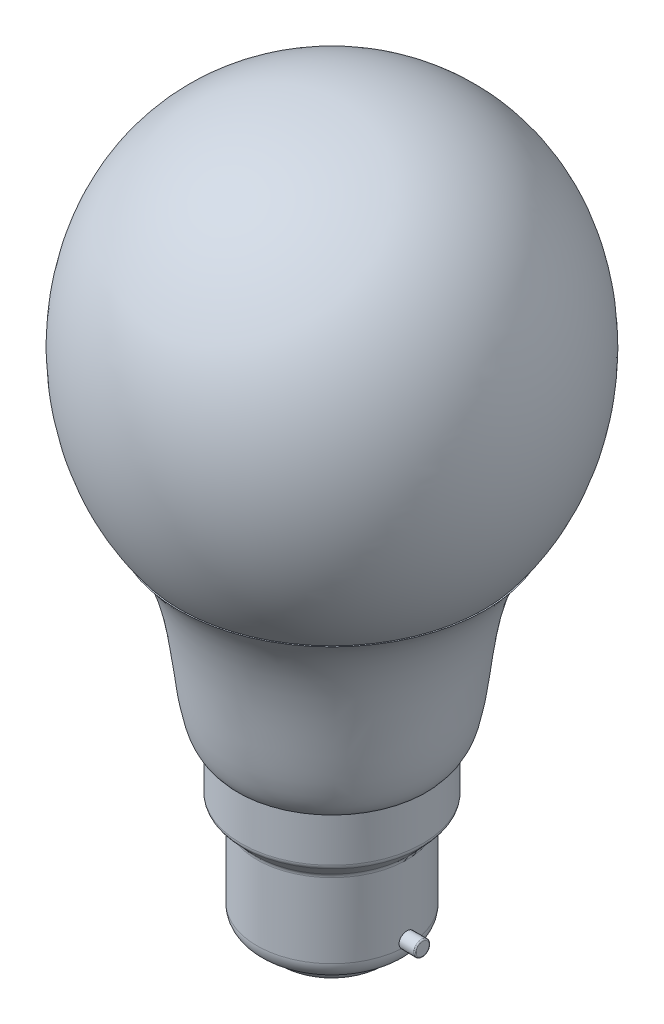
SolidWorks part; units mm, degrees
ref_plane "Front Plane" through (0, 0, 0) normal (0, 0, 1) x (1, 0, 0)
ref_plane "Top Plane" through (0, 0, 0) normal (0, 1, 0) x (1, 0, 0)
ref_plane "Right Plane" through (0, 0, 0) normal (1, 0, 0) x (0, 0, -1)
sketch "Sketch1" plane through (0, 0, 0) normal (0, 0, 1) x (1, 0, 0)
  line L0 (-312.7536, 342.4742) -> (-290.7536, 342.4742) construction
  line L1 (-11.0043, 13.5815) -> (10.9957, 13.5815) construction
  dimension "D1" = 22
  dimension "D2" = 22
sketch "Sketch2" plane through (0, 0, 0) normal (0, 0, 1) x (1, 0, 0)
  line L0 (0, 0) -> (0, 30)
  line L1 (0, 30) -> (0, 118)
  line L2 (0, 30) -> (15, 30)
  line L3 (15, 30) -> (19.4, 34.3) construction
  line L4 (19.4, 34.3) -> (16.4, 51.5) construction
  line L5 (16.4, 51.5) -> (24.5115, 60) construction
  line L6 (24.5115, 60) -> (0, 60)
  line L7 (0, 60) -> (0, 30)
  spline S0 degree 3 poles (15, 30) (19.4, 34.3) (16.4, 51.5) (24.5115, 60) knots 0 0 0 0 1 1 1 1
  point P8 (12.2557, 60)
  point P9 (0, 0)
  point P11 (0.6623, 30)
  dimension "D5" = 32
  dimension "D1" = 30
  dimension "D2" = 88
  dimension "D3" = 15
  dimension "D4" = 30
  dimension "D6" = 4.3
  dimension "D7" = 16.4
  dimension "D8" = 19.4
  dimension "D9" = 21.5
revolve "Revolve2" add sketch "Sketch2" angle 360 about L1
sketch "Sketch4" plane through (0, 0, 0) normal (0, 0, 1) x (1, 0, 0)
  line L0 (0, 60) -> (0, 118)
  line L1 (24.5115, 60) -> (-24.5115, 60) construction
  line L2 (0, 60) -> (24.3, 60)
  line L3 (0, 118) -> (32.9621, 118) construction
  line L4 (32.9621, 118) -> (40, 80) construction
  line L5 (40, 80) -> (24.3, 60) construction
  spline S0 degree 3 poles (0, 118) (32.9621, 118) (40, 80) (24.3, 60) knots 0 0 0 0 1 1 1 1
  point P8 (31.2763, 119.4939)
  point P9 (39.6236, 79.0706)
  point P10 (32.7636, 118.3221)
  point P11 (0, 0)
  point P12 (39.8683, 79.9908)
  point P15 (11.1368, 60)
  point P16 (0, 112.3974)
  point P17 (0, 68.5441)
  point P18 (0, 79.8107)
  point P19 (1.3785, 60)
  dimension "D3" = 78.5
  dimension "D1" = 58
  dimension "D2" = 24.3
  dimension "D4" = 58
  dimension "D5" = 20
  dimension "D6" = 40
revolve "Revolve3" add sketch "Sketch4" angle 360 about L0
sketch "Sketch5" plane through (0, 0, 0) normal (0, 0, 1) x (1, 0, 0)
  line L0 (0, 0) -> (0, 30)
  line L1 (-15, 30) -> (15, 30) construction
  line L2 (0, 30) -> (14.5, 30)
  line L3 (14.5, 30) -> (14.5, 22.3)
  line L4 (14.5, 22.3) -> (12, 19.6)
  line L5 (12, 19.6) -> (12, 7.3)
  line L6 (0, 4.3) -> (9, 4.3)
  line L7 (0, 2) -> (6.4924, 2)
  arc A0 (9, 4.3) -> (12, 7.3) centre (9, 7.3) ccw
  arc A1 (6.4924, 2) -> (9, 4.3) centre (6.4924, 4.5169) ccw
  dimension "D1" = 7.7
  dimension "D2" = 14.5
  dimension "D3" = 12
  dimension "D4" = 10.4
  dimension "D5" = 9
  dimension "D6" = 4.3
  dimension "D7" = 2.3
revolve "Revolve4" add sketch "Sketch5" angle 360 about L0
sketch "Sketch6" plane through (0, 0, 0) normal (0, 0, 1) x (1, 0, 0)
  line L0 (-14.5, 8.3646) -> (14.5, 8.1396)
  line L1 (-14.5, 8.3646) -> (-14.5, 9.377)
  line L2 (-14.5, 9.377) -> (14.5, 9.377)
  line L3 (14.5, 9.377) -> (14.5, 8.1396)
  line L4 (14.5, 8.1396) -> (14.4182, 8.3271)
  point P2 (0, 8.2521)
  dimension "D1" = 29
revolve "Revolve5" add sketch "Sketch6" angle 360 about L0
fillet "Fillet1" radius 0.2 2 edges at (14.4808, 6.9023, 0) (-14.5157, 7.3523, 0)
fillet "Fillet2" radius 1 2 edges at (0, 22.3, -14.5) (0, 19.6, -12)
